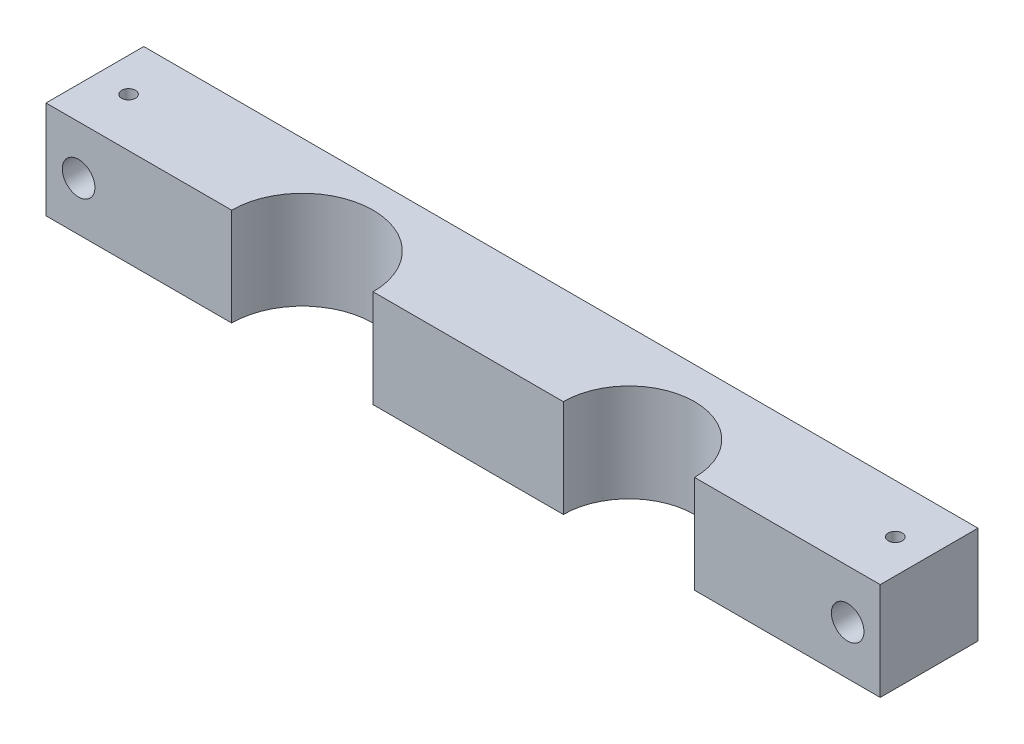
SolidWorks part; units mm, degrees
ref_plane "Front Plane" through (0, 0, 0) normal (0, 0, 1) x (1, 0, 0)
ref_plane "Top Plane" through (0, 0, 0) normal (0, 1, 0) x (1, 0, 0)
ref_plane "Right Plane" through (0, 0, 0) normal (1, 0, 0) x (0, 0, -1)
sketch "Sketch1" plane through (0, 0, 0) normal (0, 1, 0) x (1, 0, 0)
  line L0 (63.735, 0) -> (100.8062, 0)
  line L1 (0, 0) -> (36.176, 0)
  line L2 (0, 0) -> (0, 19.05)
  line L3 (0, 19.05) -> (162.56, 19.05)
  line L4 (162.56, 0) -> (162.56, 19.05)
  line L5 (126.3841, 0) -> (162.56, 0)
  line L6 (36.176, 0) -> (63.735, 0) construction
  line L7 (100.8062, 0) -> (126.3841, 0) construction
  line L8 (81.28, 19.05) -> (81.28, 0) construction
  arc A0 (63.735, 0) -> (36.176, 0) centre (49.9555, 0) ccw
  arc A1 (126.3841, 0) -> (100.8062, 0) centre (113.5951, 0) ccw
  dimension "D1" = 13.7795
  dimension "D2" = 12.7889
  dimension "D6" = 19.05
  dimension "D4" = 162.56
  dimension "D3" = 63.6397
extrude "Boss-Extrude3" add sketch "Sketch1" along normal blind 19.05 contours L2 L3 L4 L5 A1 L0 A0 L1
ref_plane "Plane1" through (81.28, 0, 0) normal (-1, 0, 0) x (0, 0, 1)
hole_wizard "1/4 (0.25) Diameter Hole1" positions "Sketch3" profile "Sketch2" hole size "1/4" standard "ANSI Inch" end condition through all
sketch "Sketch3" plane through (0, 0, 0) normal (0, 0, 1) x (1, 0, 0)
  line L2 (0, 0) -> (36.176, 0) construction
  line L4 (81.28, 10.4775) -> (81.28, -10.4775) construction
  point P0 (6.35, 9.525)
  dimension "D1" = 74.93
  dimension "D3" = 9.525
sketch "Sketch2" plane through (6.35, 9.525, 0) normal (1, 0, 0) x (0, -1, 0)
  line L0 (0, 0) -> (0, 19.05)
  line L1 (0, 19.05) -> (3.175, 19.05)
  line L2 (3.175, 19.05) -> (3.175, 0)
  line L5 (3.175, 0) -> (0, 0)
  line L11 (0, -6.35) -> (0, 107.95) construction
  dimension "Thru Hole Dia." = 6.35
  dimension "Thru Hole Depth" = 19.05
hole_wizard "#6-32 Tapped Hole1" positions "Sketch6" profile "Sketch4" tap size "#6-32" standard "ANSI Inch"
sketch "Sketch6" plane through (0, 19.05, 0) normal (0, 1, 0) x (1, 0, 0)
  line L0 (0, 0) -> (0, 19.05) construction
  line L2 (0, 0) -> (36.176, 0) construction
  point P0 (6.5789, 9.5088)
  point P14 (6.023, 0)
  dimension "D1" = 9.525
  dimension "D2" = 6.5789
sketch "Sketch4" plane through (6.5789, 19.05, -9.5088) normal (1, 0, 0) x (0, 0, 1)
  line L0 (0, 0) -> (0, 19.05)
  line L1 (0, 19.05) -> (1.3525, 19.05)
  line L2 (1.3525, 19.05) -> (1.3525, 0)
  line L5 (1.3525, 0) -> (0, 0)
  line L11 (0, -6.35) -> (0, 107.95) construction
  dimension "Thru Tap Drill Dia." = 2.7051
  dimension "Thru Tap Drill Depth" = 19.05
cosmetic thread "Hole Thread1"
mirror "Mirror1" about plane through (81.28, 0, 0) normal (-1, 0, 0) of "#6-32 Tapped Hole1", "1/4 (0.25) Diameter Hole1"
